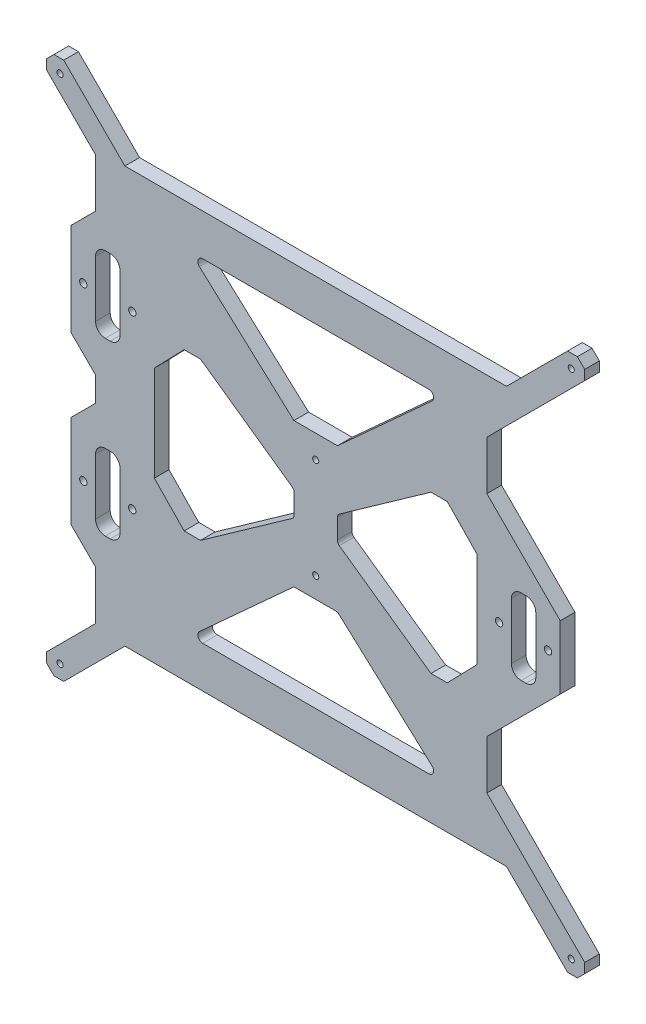
SolidWorks part; units mm, degrees
material "Lega 1060"
ref_plane "Piano frontale" through (0, 0, 0) normal (0, 0, 1) x (1, 0, 0)
ref_plane "Piano superiore" through (0, 0, 0) normal (0, 1, 0) x (1, 0, 0)
ref_plane "Piano destro" through (0, 0, 0) normal (1, 0, 0) x (0, 0, -1)
sketch "FRAME" plane through (0, 0, 0) normal (0, 0, 1) x (1, 0, 0)
  line L38 (65, 325) -> (63, 325)
  line L39 (63, 325) -> (60, 322)
  line L40 (60, 322) -> (60, 320)
  line L41 (60, 320) -> (60, 318)
  line L42 (60, 318) -> (80, 298)
  line L43 (80, 298) -> (80, 278)
  line L44 (80, 278) -> (70, 268)
  line L45 (70, 162) -> (80, 152)
  line L46 (60, 112) -> (80, 132)
  line L47 (80, 132) -> (80, 152)
  line L48 (60, 112) -> (60, 108)
  line L49 (60, 108) -> (63, 105)
  line L50 (63, 105) -> (65, 105)
  line L51 (275, 105) -> (277, 105)
  line L52 (277, 105) -> (280, 108)
  line L53 (280, 321) -> (280, 322)
  line L54 (280, 322) -> (277, 325)
  line L55 (280, 318) -> (240, 278)
  line L56 (270, 228) -> (260, 238)
  line L57 (260, 238) -> (240, 258)
  line L58 (240, 258) -> (240, 278)
  line L59 (270, 202) -> (260, 192)
  line L60 (260, 192) -> (240, 172)
  line L61 (280, 112) -> (260, 132)
  line L62 (260, 132) -> (240, 152)
  line L63 (240, 152) -> (240, 172)
  line L64 (273, 325) -> (250, 302)
  line L65 (161.2166, 218.9648) -> (161.2166, 211.0352)
  line L66 (122.4711, 279.6004) -> (161.1147, 244.4358)
  line L67 (161.1147, 244.4358) -> (178.9347, 244.4358)
  line L68 (273, 105) -> (248, 130)
  line L69 (104.0376, 234.4981) -> (104.0376, 195.5019)
  line L70 (92, 300) -> (248, 300)
  line L71 (92, 130) -> (248, 130)
  line L72 (70, 230) -> (80, 220)
  line L73 (80, 220) -> (80, 210)
  line L74 (80, 210) -> (70, 200)
  line L75 (104.0376, 234.4981) -> (116.2302, 247.0905)
  line L76 (116.2302, 247.0905) -> (122.9095, 247.0905)
  line L77 (122.9095, 247.0905) -> (160.3714, 220.5977)
  line L78 (217.1399, 247.0905) -> (179.678, 220.5977)
  line L79 (223.8192, 247.0905) -> (217.1399, 247.0905)
  line L80 (236.0117, 234.4981) -> (223.8192, 247.0905)
  line L81 (236.0117, 234.4981) -> (236.0117, 195.5019)
  line L82 (236.0117, 195.5019) -> (223.8192, 182.9095)
  line L83 (223.8192, 182.9095) -> (217.1399, 182.9095)
  line L84 (217.1399, 182.9095) -> (179.678, 209.4023)
  line L85 (178.8328, 218.9648) -> (178.8328, 211.0352)
  line L86 (122.9095, 182.9095) -> (160.3714, 209.4023)
  line L87 (104.0376, 195.5019) -> (116.2302, 182.9095)
  line L88 (116.2302, 182.9095) -> (122.9095, 182.9095)
  line L89 (123.8171, 283.0796) -> (216.2322, 283.0796)
  line L90 (217.5783, 279.6004) -> (178.9347, 244.4358)
  line L91 (65, 325) -> (67, 325)
  line L92 (277, 325) -> (273, 325)
  line L93 (280, 321) -> (280, 318)
  line L94 (280, 112) -> (280, 108)
  line L95 (273, 105) -> (275, 105)
  line L96 (67, 105) -> (65, 105)
  line L97 (217.5783, 150.3996) -> (178.9347, 185.5642)
  line L98 (250, 302) -> (248, 300)
  line L99 (161.1147, 185.5642) -> (178.9347, 185.5642)
  line L100 (67, 325) -> (92, 300)
  line L101 (122.4711, 150.3996) -> (161.1147, 185.5642)
  line L102 (123.8171, 146.9204) -> (216.2322, 146.9204)
  line L103 (67, 105) -> (92, 130)
  line L175 (70, 268) -> (70, 230)
  line L176 (70, 200) -> (70, 162)
  line L177 (270, 228) -> (270, 202)
  line L184 (80, 169) -> (80, 192)
  line L185 (84, 196) -> (86, 196)
  line L186 (90, 192) -> (90, 169)
  line L187 (86, 165) -> (84, 165)
  line L188 (80, 239.007) -> (80, 262.007)
  line L189 (84, 266.007) -> (86, 266.007)
  line L190 (90, 262.007) -> (90, 239.007)
  line L191 (86, 235.007) -> (84, 235.007)
  line L192 (250, 202.8629) -> (250, 225.8629)
  line L193 (254, 229.8629) -> (256, 229.8629)
  line L194 (260, 225.8629) -> (260, 202.8629)
  line L195 (256, 198.8629) -> (254, 198.8629)
  line L201 (80, 215) -> (297.8607, 215) construction
  line L202 (170.0247, 235) -> (170.0247, 194) construction
  circle A6 centre (75, 250) radius 1.5
  circle A7 centre (95.0376, 250) radius 1.5
  circle A8 centre (75, 180) radius 1.5
  circle A9 centre (95, 180) radius 1.5
  circle A10 centre (265, 215) radius 1.5
  circle A11 centre (245, 215) radius 1.5
  circle A12 centre (65.5, 319.5) radius 1.25
  circle A13 centre (274.5, 110.5) radius 1.25
  circle A14 centre (274.5, 319.5) radius 1.25
  circle A15 centre (65.5, 110.5) radius 1.25
  arc A22 (84, 196) -> (80, 192) centre (84, 192) ccw
  arc A23 (90, 192) -> (86, 196) centre (86, 192) ccw
  arc A24 (80, 169) -> (84, 165) centre (84, 169) ccw
  arc A25 (86, 165) -> (90, 169) centre (86, 169) ccw
  circle A36 centre (170.0247, 194) radius 1.25
  circle A37 centre (170.0247, 235) radius 1.25
  arc A38 (86, 235.007) -> (90, 239.007) centre (86, 239.007) ccw
  arc A39 (84, 266.007) -> (80, 262.007) centre (84, 262.007) ccw
  arc A40 (90, 262.007) -> (86, 266.007) centre (86, 262.007) ccw
  arc A41 (80, 239.007) -> (84, 235.007) centre (84, 239.007) ccw
  arc A42 (256, 198.8629) -> (260, 202.8629) centre (256, 202.8629) ccw
  arc A43 (254, 229.8629) -> (250, 225.8629) centre (254, 225.8629) ccw
  arc A44 (260, 225.8629) -> (256, 229.8629) centre (256, 225.8629) ccw
  arc A45 (250, 202.8629) -> (254, 198.8629) centre (254, 202.8629) ccw
  arc A48 (122.4711, 279.6004) -> (123.8171, 283.0796) centre (123.8171, 281.0796) cw
  arc A49 (123.8171, 146.9204) -> (122.4711, 150.3996) centre (123.8171, 148.9204) cw
  arc A52 (217.5783, 279.6004) -> (216.2322, 283.0796) centre (216.2322, 281.0796) ccw
  arc A53 (216.2322, 146.9204) -> (217.5783, 150.3996) centre (216.2322, 148.9204) ccw
  arc A54 (178.8328, 218.9648) -> (179.678, 220.5977) centre (180.8328, 218.9648) cw
  arc A55 (178.8328, 211.0352) -> (179.678, 209.4023) centre (180.8328, 211.0352) ccw
  arc A56 (161.2166, 218.9648) -> (160.3714, 220.5977) centre (159.2166, 218.9648) ccw
  arc A57 (160.3714, 209.4023) -> (161.2166, 211.0352) centre (159.2166, 211.0352) ccw
  point P105 (236.0117, 215)
  point P112 (104.0376, 215)
  point P117 (170.0247, 244.4358)
  point P118 (170.0247, 283.0796)
  point P301 (118.6476, 283.0796)
  point P320 (118.6476, 146.9204)
  point P323 (221.4017, 283.0796)
  point P326 (221.4017, 146.9204)
  point P329 (178.8328, 220)
  point P332 (178.8328, 210)
  point P335 (161.2166, 220)
  point P338 (161.2166, 210)
  dimension "D1" = 2
  dimension "D2" = 2.5
  dimension "D3" = 2
  dimension "D4" = 2
  dimension "D5" = 2
  dimension "D6" = 2
  dimension "D7" = 2
  dimension "D8" = 2.5
  dimension "D9" = 2.5
  dimension "D10" = 2.5
  dimension "D11" = 2.5
  dimension "D12" = 2.5
sketch "ANCORS" [suppressed] plane through (0, 0, 0) normal (0, 0, 1) x (1, 0, 0)
  line L1 (170.0247, 235) -> (170.0247, 194) construction
  line L2 (170.0247, 214.5) -> (158.9936, 214.5) construction
  circle A0 centre (120.7826, 212.556) radius 2
  circle A1 centre (216.1502, 212.556) radius 2
  circle A2 centre (167.2683, 270.0641) radius 2
  circle A3 centre (167.2683, 156.9648) radius 2
  circle A4 centre (120.7826, 90.4425) radius 2
  circle A5 centre (216.1502, 90.4425) radius 2
  circle A6 centre (170.0247, 214.5) radius 2
  dimension "D1" = 4
extrude "Boss-Extrude1" add sketch "FRAME" along normal blind 6
